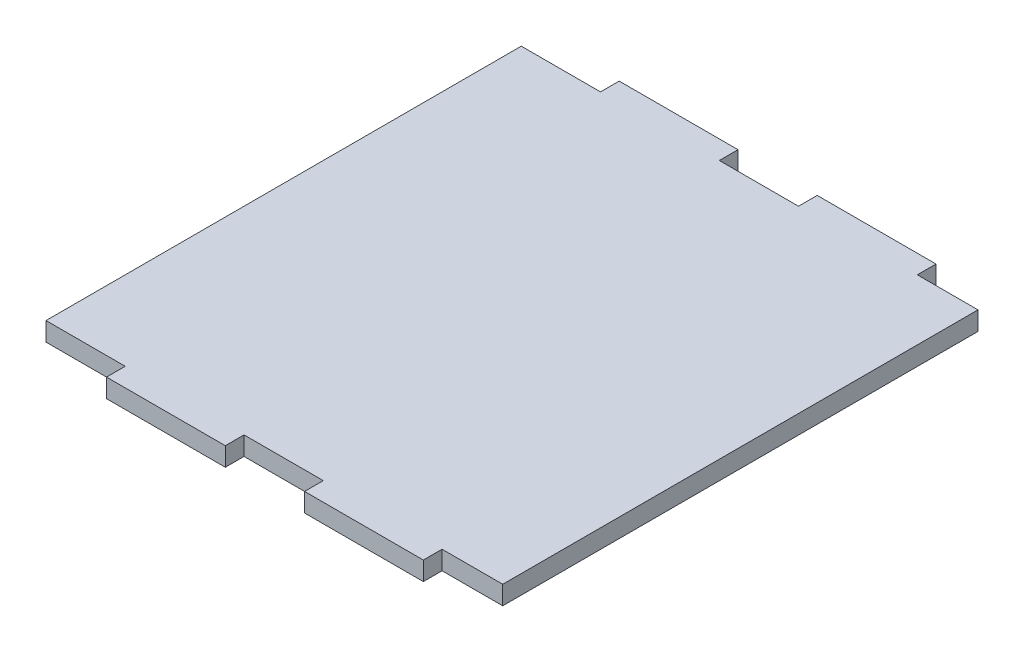
SolidWorks part; units mm, degrees
ref_plane "Front Plane" through (0, 0, 0) normal (0, 0, 1) x (1, 0, 0)
ref_plane "Top Plane" through (0, 0, 0) normal (0, 1, 0) x (1, 0, 0)
ref_plane "Right Plane" through (0, 0, 0) normal (1, 0, 0) x (0, 0, -1)
sketch "Sketch1" plane through (0, 0, 0) normal (0, 1, 0) x (1, 0, 0)
  line L0 (-25.4, 41.1) -> (-6.35, 41.1)
  line L1 (-25.4, -41.1) -> (-6.35, -41.1)
  line L2 (-38.1, 38.1) -> (-38.1, -38.1)
  line L3 (-38.1, -38.1) -> (-25.4, -38.1)
  line L4 (-25.4, -38.1) -> (-25.4, -41.1)
  line L5 (-6.35, -38.1) -> (-6.35, -41.1)
  line L6 (6.35, -38.1) -> (6.35, -41.1)
  line L7 (25.4, -38.1) -> (25.4, -41.1)
  line L8 (6.35, -41.1) -> (25.4, -41.1)
  line L9 (-119.8539, 0) -> (200.76, 0) construction
  line L10 (-6.35, -38.1) -> (6.35, -38.1)
  line L11 (25.4, -38.1) -> (35.1275, -38.1)
  line L12 (25.4, 38.1) -> (25.4, 41.1)
  line L13 (6.35, 41.1) -> (25.4, 41.1)
  line L14 (6.35, 38.1) -> (6.35, 41.1)
  line L15 (-6.35, 38.1) -> (-6.35, 41.1)
  line L16 (35.1275, 38.1) -> (35.1275, -38.1)
  line L17 (-25.4, 38.1) -> (-25.4, 41.1)
  line L18 (-38.1, 38.1) -> (-25.4, 38.1)
  line L19 (-6.35, 38.1) -> (6.35, 38.1)
  line L20 (25.4, 38.1) -> (35.1275, 38.1)
  dimension "D5" = 12.7
  dimension "D6" = 19.05
  dimension "D7" = 12.7
  dimension "D8" = 19.05
  dimension "D1" = 41.1
  dimension "D3" = 38.1
  dimension "D4" = 3
extrude "Boss-Extrude1" add sketch "Sketch1" along normal blind 3
